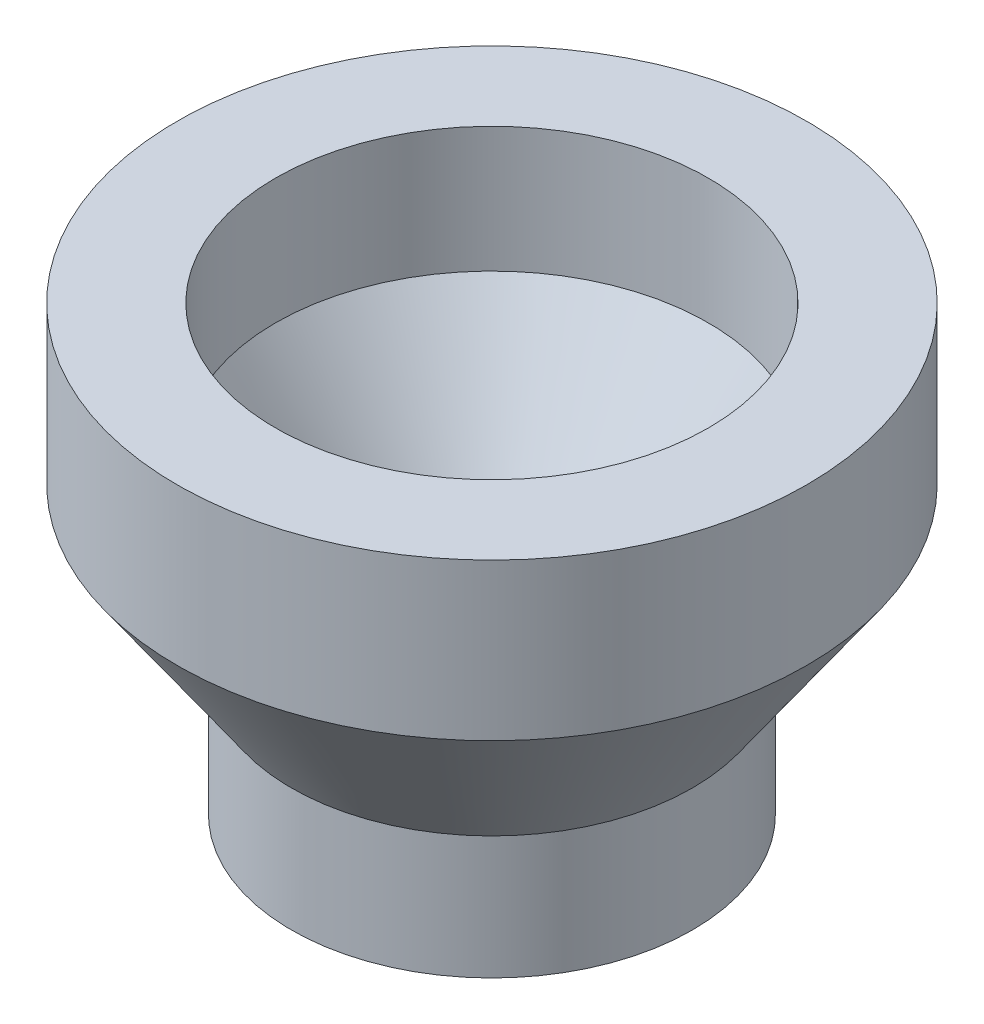
SolidWorks part; units mm, degrees
ref_plane "Front Plane" through (0, 0, 0) normal (0, 0, 1) x (1, 0, 0)
ref_plane "Top Plane" through (0, 0, 0) normal (0, 1, 0) x (1, 0, 0)
ref_plane "Right Plane" through (0, 0, 0) normal (1, 0, 0) x (0, 0, -1)
sketch "Sketch1" plane through (0, 0, 0) normal (0, 0, 1) x (1, 0, 0)
  line L0 (-2.575, 34.7901) -> (-4.075, 34.7901)
  line L1 (-4.075, 34.7901) -> (-4.075, 37.2901)
  line L2 (-4.075, 37.2901) -> (-6.4, 40.6106)
  line L3 (-6.4, 40.6106) -> (-6.4, 43.7901)
  line L4 (-6.4, 43.7901) -> (-4.4, 43.7901)
  line L5 (-4.4, 43.7901) -> (-4.4, 41.2412)
  line L6 (-4.4, 41.2412) -> (-2.575, 38.6348)
  line L7 (-2.575, 38.6348) -> (-2.575, 34.7901)
  line L8 (0, 9.7901) -> (0, 52.7901) construction
  point P2 (-24.0082, 47.4612)
  point P20 (-2.575, 25)
  point P23 (-4.4, 34.0029)
  point P24 (-4.4, 34.0013)
  point P25 (-4.4, 33.8988)
  point P26 (-4.4, 33.996)
  point P28 (-4.4, 33.9723)
  point P30 (-2.575, 28.4536)
  point P31 (-4.4, 31.4213)
  point P32 (-4.4, 30.8204)
  dimension "D1" = 2
  dimension "D2" = 12.8
  dimension "D3" = 2
  dimension "D4" = 5.15
  dimension "D5" = 2.5
  dimension "D6" = 1.5
  dimension "D7" = 35
revolve "Revolve1" add sketch "Sketch1" angle 360 about L8
